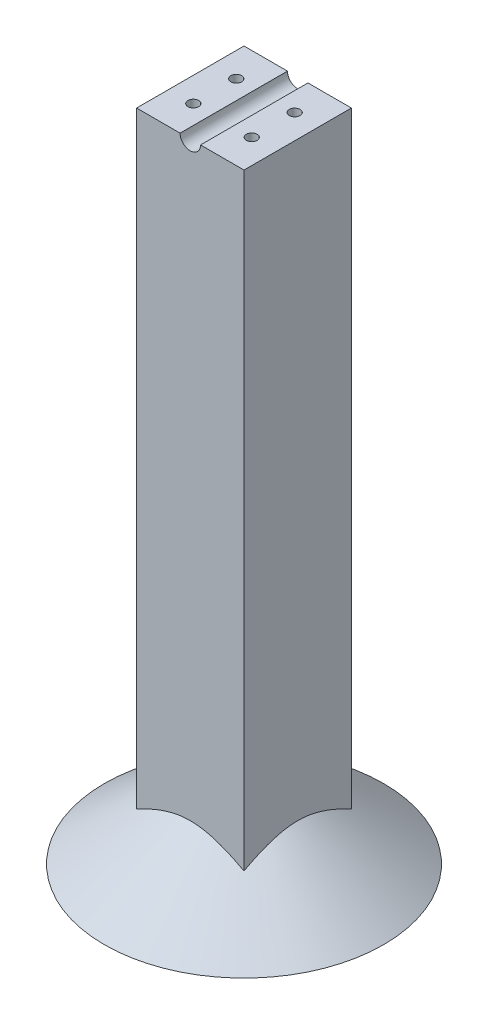
SolidWorks part; units mm, degrees
ref_plane "Front Plane" through (0, 0, 0) normal (0, 0, 1) x (1, 0, 0)
ref_plane "Top Plane" through (0, 0, 0) normal (0, 1, 0) x (1, 0, 0)
ref_plane "Right Plane" through (0, 0, 0) normal (1, 0, 0) x (0, 0, -1)
sketch "Sketch1" plane through (0, 0, 0) normal (0, 1, 0) x (1, 0, 0)
  line L1 (-12.5, 12.5) -> (12.5, 12.5)
  line L2 (-12.5, 12.5) -> (-12.5, -12.5)
  line L3 (-12.5, -12.5) -> (12.5, -12.5)
  line L4 (12.5, 12.5) -> (12.5, -12.5)
  line L5 (-12.5, 12.5) -> (12.5, -12.5) construction
  line L6 (-12.5, -12.5) -> (12.5, 12.5) construction
  point P0 (0, 0)
  dimension "D1" = 25
  dimension "D2" = 25
extrude "Boss-Extrude1" add sketch "Sketch1" against normal blind 152.4
sketch "Sketch2" plane through (0, 0, 0) normal (0, 0, 1) x (1, 0, 0)
  line L0 (0, -152.4) -> (0, 0) construction
  line L1 (12.5, -152.4) -> (-12.5, -152.4) construction
  line L2 (12.5, 0) -> (-12.5, 0) construction
  line L3 (12.5, -137.4) -> (32.5, -152.4)
  line L4 (12.5, -152.4) -> (12.5, 0) construction
  line L5 (32.5, -152.4) -> (12.5, -152.4)
  line L6 (12.5, -152.4) -> (12.5, -137.4)
  dimension "D1" = 20
  dimension "D2" = 15
revolve "Revolve1" add sketch "Sketch2" angle 360 about L0
sketch "Sketch3" plane through (0, 0, 12.5) normal (0, 0, 1) x (1, 0, 0)
  circle A0 centre (0, 0) radius 2.3813
  dimension "D1" = 4.7625
extrude "Cut-Extrude1" cut sketch "Sketch3" against normal up to next
sketch "Sketch4" plane through (0, 0, 0) normal (0, 1, 0) x (1, 0, 0)
  line L0 (12.5, 0) -> (-12.5, 0) construction
  line L1 (12.5, -12.5) -> (12.5, 12.5) construction
  line L2 (-12.5, 12.5) -> (-12.5, -12.5) construction
  line L3 (0, 12.5) -> (0, -12.5) construction
  line L4 (12.5, 12.5) -> (-12.5, 12.5) construction
  line L5 (-12.5, -12.5) -> (12.5, -12.5) construction
  line L6 (-6.8, 5) -> (6.8, 5) construction
  circle A0 centre (-6.8, 5) radius 1
  circle A1 centre (6.8, 5) radius 1
  circle A2 centre (6.8, -5) radius 1
  circle A3 centre (-6.8, -5) radius 1
  point P14 (0, 5)
  dimension "D2" = 2
  dimension "D3" = 2
  dimension "D1" = 5
  dimension "D4" = 6.8
extrude "Cut-Extrude2" cut sketch "Sketch4" against normal blind 10
hole_wizard "Tap Drill for M3x0.5 Tap1" positions "Sketch5" profile "Sketch6" hole size "M3x0.5" standard "ANSI Metric"
sketch "Sketch5" plane through (0, 0, 0) normal (0, 1, 0) x (1, 0, 0)
  point P0 (-6.8, -5)
  point P3 (-6.8, 5)
  point P6 (6.8, 5)
  point P9 (6.8, -5)
sketch "Sketch6" plane through (-6.8, 0, 5) normal (1, 0, 0) x (0, 0, 1)
  line L0 (0, 0) -> (0, 15.7511)
  line L1 (0, 15.7511) -> (1.25, 15)
  line L2 (1.25, 15) -> (1.25, 0)
  line L5 (1.25, 0) -> (0, 0)
  line L10 (0, 15.7511) -> (-1.25, 15) construction
  line L11 (0, -6.35) -> (0, 107.95) construction
  dimension "Hole Dia." = 2.5
  dimension "Hole Depth" = 15
  dimension "Drill Angle" = 118
